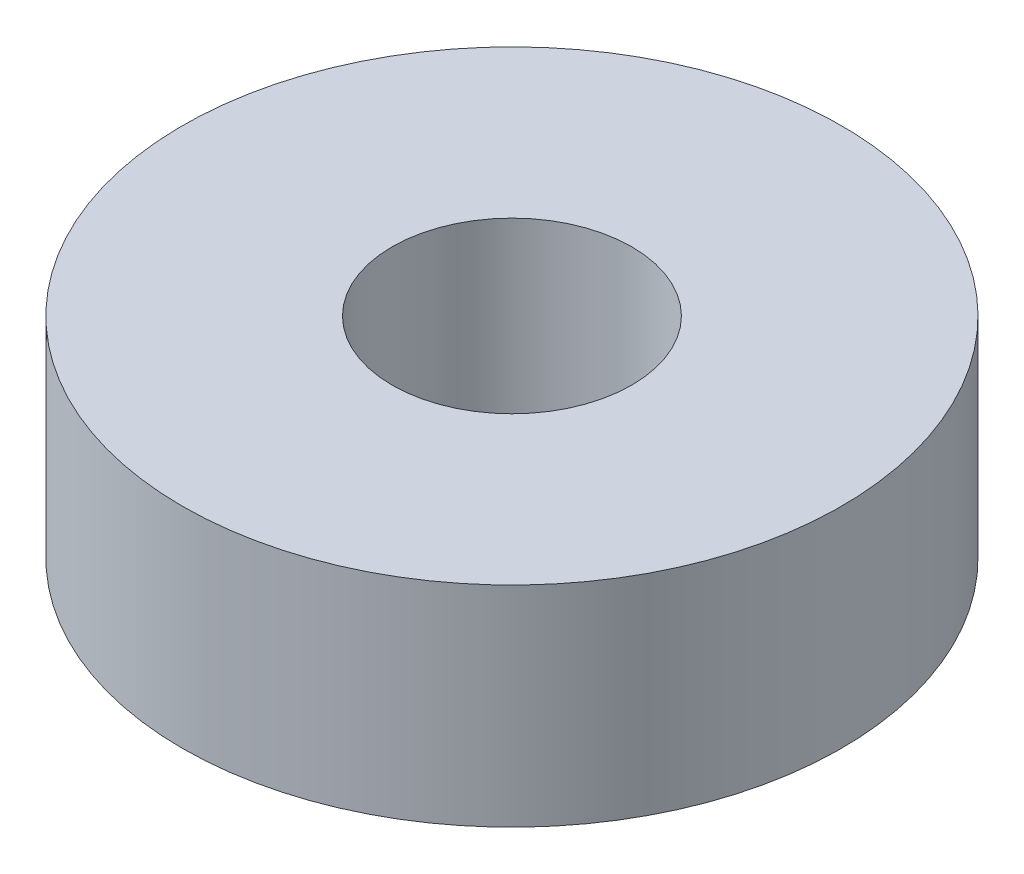
SolidWorks part; units mm, degrees
ref_plane "Plano frontal" through (0, 0, 0) normal (0, 0, 1) x (1, 0, 0)
ref_plane "Plano superior" through (0, 0, 0) normal (0, 1, 0) x (1, 0, 0)
ref_plane "Plano direito" through (0, 0, 0) normal (1, 0, 0) x (0, 0, -1)
sketch "Esboço1" plane through (0, 0, 0) normal (0, 1, 0) x (1, 0, 0)
  circle A0 centre (0, 0) radius 11
  circle A1 centre (0, 0) radius 4
extrude "Ressalto-extrusão1" add sketch "Esboço1" along normal blind 7
